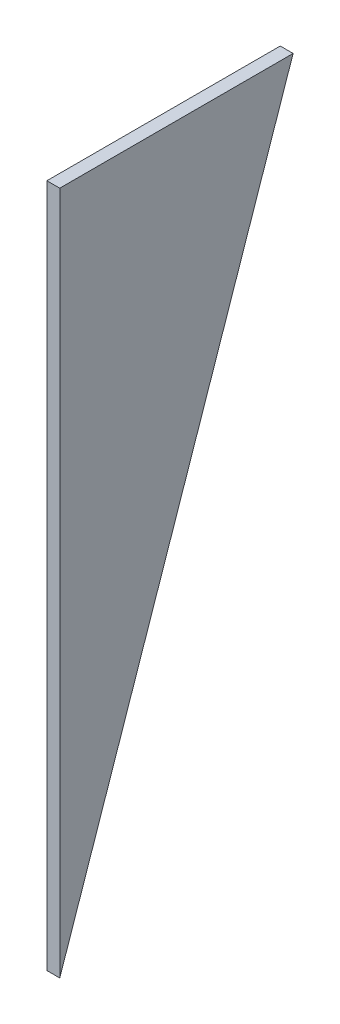
SolidWorks part; units mm, degrees
ref_plane "Front Plane" through (0, 0, 0) normal (0, 0, 1) x (1, 0, 0)
ref_plane "Top Plane" through (0, 0, 0) normal (0, 1, 0) x (1, 0, 0)
ref_plane "Right Plane" through (0, 0, 0) normal (1, 0, 0) x (0, 0, -1)
sketch "Sketch1" plane through (0, 0, 0) normal (1, 0, 0) x (0, 0, -1)
  line L0 (290, 850) -> (0, 0)
  line L2 (0, 0) -> (0, 850)
  line L3 (0, 850) -> (290, 850)
  dimension "D1" = 850
  dimension "D2" = 290
  dimension "D3" = 898.1091
extrude "Extrude2" add sketch "Sketch1" along normal blind 16
